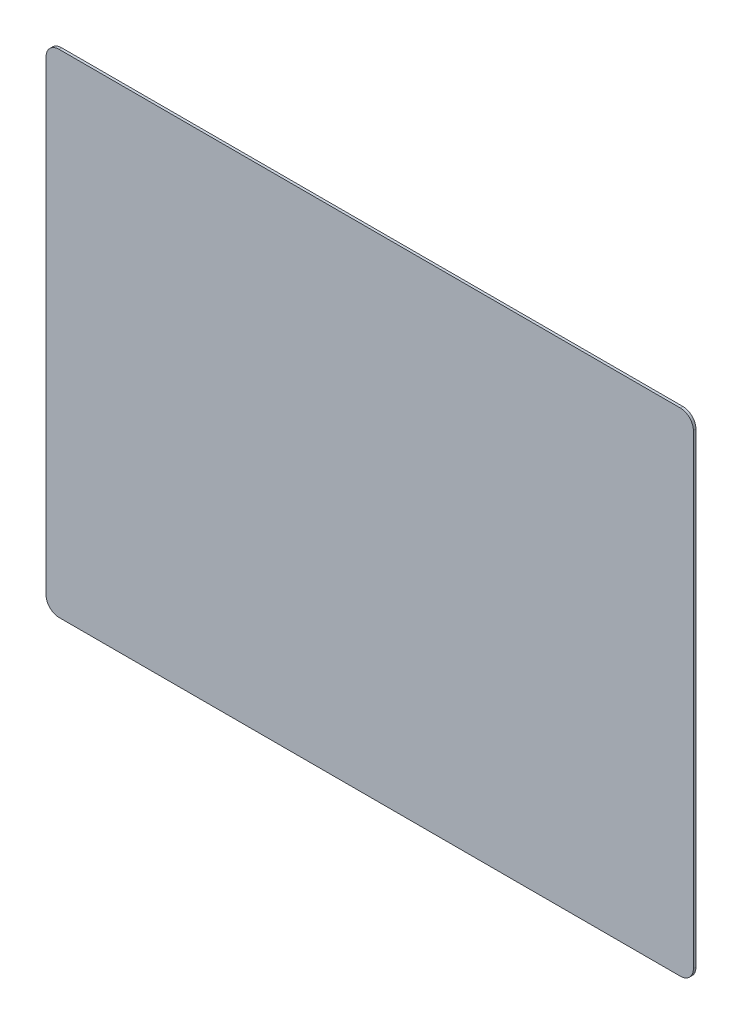
SolidWorks part; units mm, degrees
material "Acrylic (Medium-high impact)"
ref_plane "Front Plane" through (0, 0, 0) normal (0, 0, 1) x (1, 0, 0)
ref_plane "Top Plane" through (0, 0, 0) normal (0, 1, 0) x (1, 0, 0)
ref_plane "Right Plane" through (0, 0, 0) normal (1, 0, 0) x (0, 0, -1)
sketch "Sketch1" plane through (0, 0, 0) normal (0, 0, 1) x (1, 0, 0)
  line L1 (-493.5, -374) -> (493.5, -374) construction
  line L2 (-493.5, -374) -> (-493.5, 374) construction
  line L3 (-493.5, 374) -> (493.5, 374) construction
  line L4 (493.5, -374) -> (493.5, 374) construction
  line L5 (-493.5, -374) -> (493.5, 374) construction
  line L6 (-493.5, 374) -> (493.5, -374) construction
  line L7 (-498.5, -379) -> (498.5, -379)
  line L8 (-498.5, -379) -> (-498.5, 379)
  line L9 (-498.5, 379) -> (498.5, 379)
  line L10 (498.5, -379) -> (498.5, 379)
  line L11 (-498.5, -379) -> (498.5, 379) construction
  line L12 (-498.5, 379) -> (498.5, -379) construction
  point P0 (0, 0)
  dimension "D1" = 987
  dimension "D2" = 748
  dimension "D3" = 5
  dimension "D4" = 5
extrude "Boss-Extrude1" add sketch "Sketch1" along normal blind 4
fillet "Fillet1" radius 20 4 edges at (-498.5, -379, 2) (-498.5, 379, 2) (498.5, 379, 2) (498.5, -379, 2)
